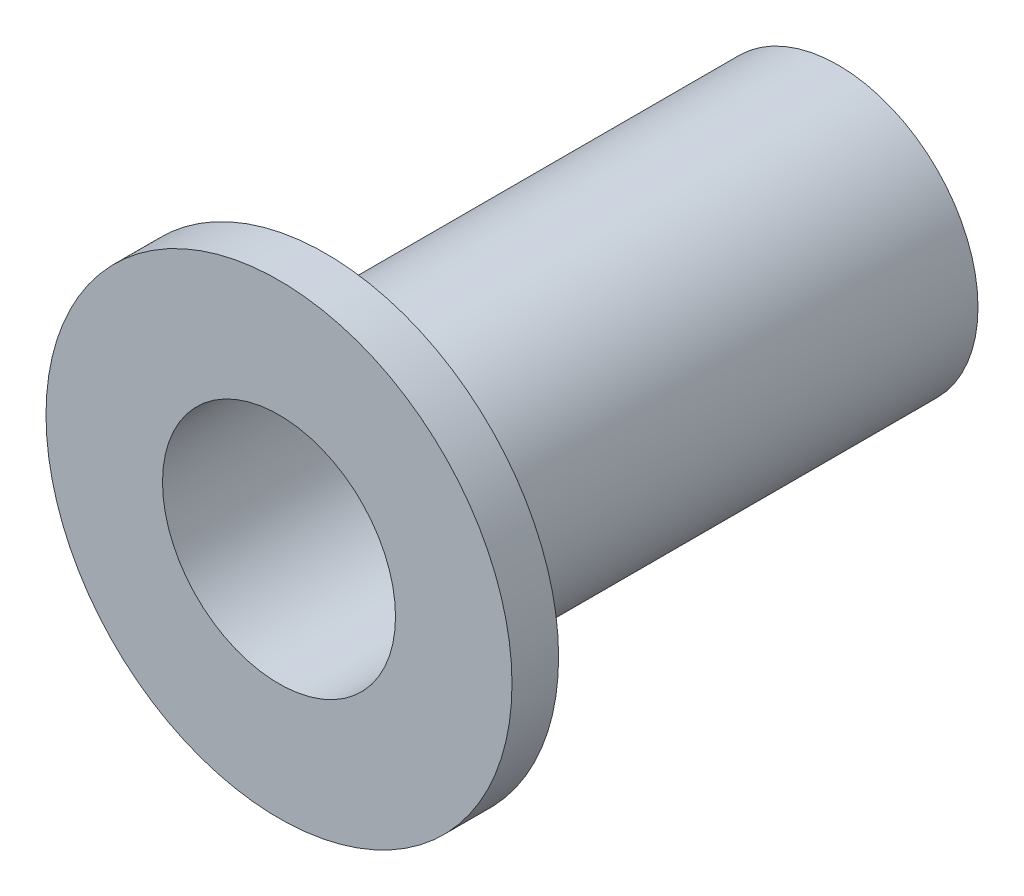
SolidWorks part; units mm, degrees
material "Brass"
ref_plane "Front Plane" through (0, 0, 0) normal (0, 0, 1) x (1, 0, 0)
ref_plane "Top Plane" through (0, 0, 0) normal (0, 1, 0) x (1, 0, 0)
ref_plane "Right Plane" through (0, 0, 0) normal (1, 0, 0) x (0, 0, -1)
sketch "Sketch1" plane through (0, 0, 0) normal (0, 0, 1) x (1, 0, 0)
  circle A0 centre (0, 0) radius 1.25
  circle A1 centre (0, 0) radius 1.5
  dimension "D1" = 2.5
  dimension "D2" = 3
extrude "Boss-Extrude1" add sketch "Sketch1" along normal blind 6
sketch "Sketch2" plane through (0, 0, 6) normal (0, 0, 1) x (1, 0, 0)
  circle A0 centre (0, 0) radius 2.5
  circle A1 centre (0, 0) radius 1.25
  dimension "D1" = 5
extrude "Boss-Extrude2" add sketch "Sketch2" against normal blind 0.5
